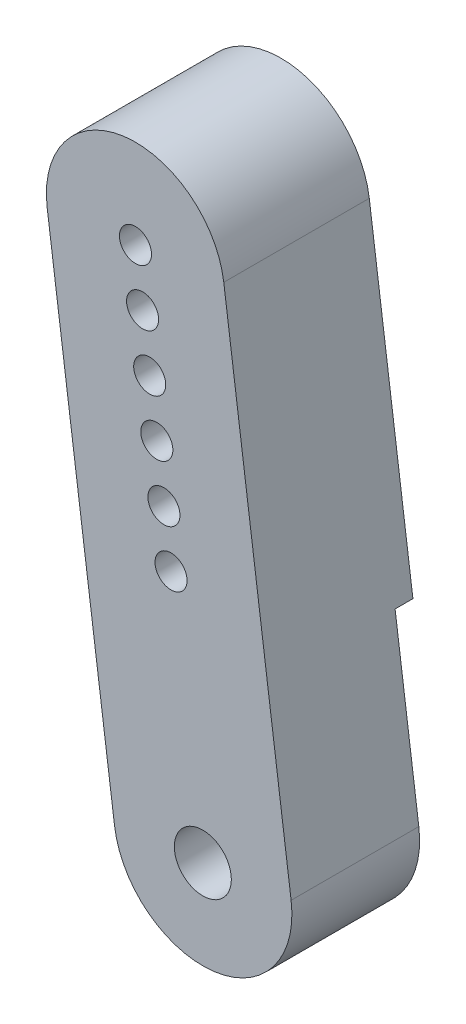
SolidWorks part; units mm, degrees
ref_plane "Front Plane" through (0, 0, 0) normal (0, 0, 1) x (1, 0, 0)
ref_plane "Top Plane" through (0, 0, 0) normal (0, 1, 0) x (1, 0, 0)
ref_plane "Right Plane" through (0, 0, 0) normal (1, 0, 0) x (0, 0, -1)
sketch "Sketch1" plane through (0, 0, 0) normal (0, 0, 1) x (1, 0, 0)
  line L0 (-8.7357, 27.4818) -> (-4.9555, -0.6655) construction
  line L3 (-4.9555, -0.6655) -> (-8.7357, 27.4818)
  line L4 (1.1753, 28.8128) -> (4.9555, 0.6655)
  arc A0 (-4.9555, -0.6655) -> (4.9555, 0.6655) centre (0, 0) ccw construction
  arc A1 (1.1753, 28.8128) -> (-8.7357, 27.4818) centre (-3.7802, 28.1473) ccw construction
  arc A2 (-8.7357, 27.4818) -> (1.1753, 28.8128) centre (-3.7802, 28.1473) cw
  arc A3 (4.9555, 0.6655) -> (-4.9555, -0.6655) centre (0, 0) cw
  dimension "D1" = 10
  dimension "D2" = 28.4
extrude "Boss-Extrude1" add sketch "Sketch1" along normal up to surface (7.1671 mm away) from offset 2.9
sketch "Sketch2" plane through (0, 0, 2.9) normal (0, 0, -1) x (-1, 0, 0)
  line L0 (-3.6245, 10.5765) -> (-1.1753, 28.8128)
  line L1 (-4.9555, 0.6655) -> (-1.1753, 28.8128) construction
  line L2 (8.7357, 27.4818) -> (6.2866, 9.2455)
  line L3 (8.7357, 27.4818) -> (4.9555, -0.6655) construction
  line L4 (6.2866, 9.2455) -> (-3.6245, 10.5765)
  arc A1 (-1.1753, 28.8128) -> (8.7357, 27.4818) centre (3.7802, 28.1473) cw
  circle A2 centre (0, 0) radius 9.825 construction
  dimension "D1" = 10
extrude "Boss-Extrude2" add sketch "Sketch2" along normal blind 1
sketch "Sketch3" plane through (0, 0, 1.9) normal (0, 0, -1) x (-1, 0, 0)
  circle A0 centre (3.7802, 28.1473) radius 0.9
  circle A1 centre (3.3809, 25.174) radius 0.9
  circle A2 centre (2.9815, 22.2007) radius 0.9
  circle A3 centre (2.5822, 19.2274) radius 0.9
  circle A4 centre (2.1829, 16.2541) radius 0.9
  circle A5 centre (1.7836, 13.2808) radius 0.9
  dimension "D1" = 1.8
  dimension "D2" = 6
extrude "Cut-Extrude1" cut sketch "Sketch3" against normal up to next
sketch "Sketch4" plane through (0, 0, 2.9) normal (0, 0, -1) x (-1, 0, 0)
  circle A0 centre (0, 0) radius 1.6
  dimension "D1" = 3.2
extrude "Cut-Extrude2" cut sketch "Sketch4" against normal up to next
